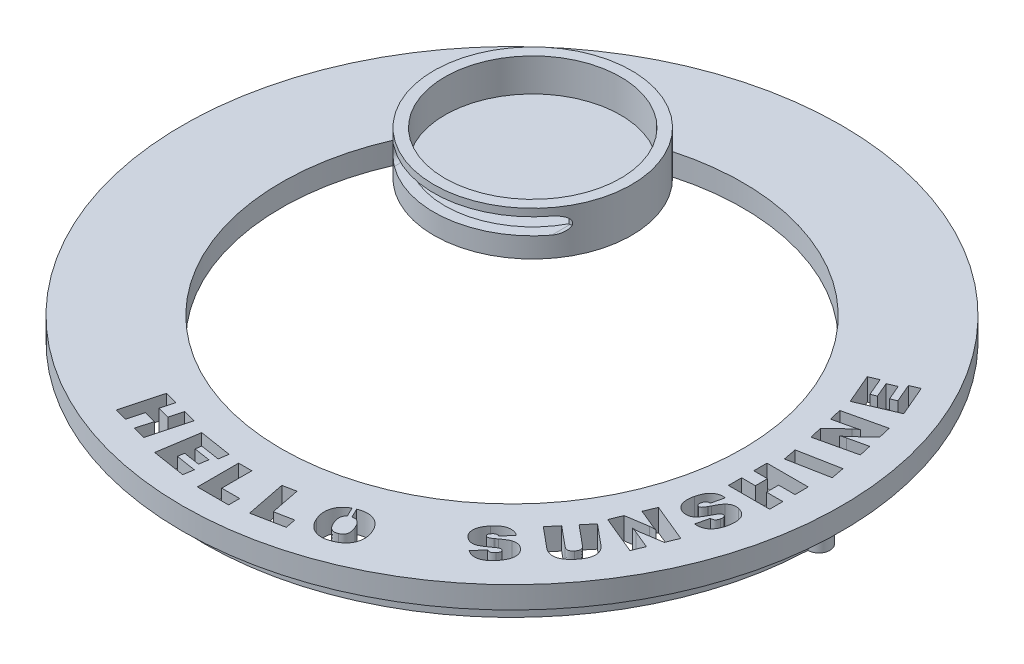
SolidWorks part; units mm, degrees
ref_plane "Front Plane" through (0, 0, 0) normal (0, 0, 1) x (1, 0, 0)
ref_plane "Top Plane" through (0, 0, 0) normal (0, 1, 0) x (1, 0, 0)
ref_plane "Right Plane" through (0, 0, 0) normal (1, 0, 0) x (0, 0, -1)
sketch "Sketch1" plane through (0, 0, 0) normal (0, 1, 0) x (1, 0, 0)
  circle A0 centre (0, 0) radius 30
extrude "Boss-Extrude1" add sketch "Sketch1" along normal blind 2
sketch "Sketch2" plane through (0, 2, 0) normal (0, 1, 0) x (1, 0, 0)
  circle A1 centre (0, 0) radius 21
extrude "Cut-Extrude1" cut sketch "Sketch2" against normal blind 2
sketch "Sketch11" plane through (0, 0, 0) normal (0, 1, 0) x (1, 0, 0)
  circle A0 centre (-11.8757, 13.7636) radius 9
extrude "Boss-Extrude3" add sketch "Sketch11" along normal blind 4
sketch "Sketch13" plane through (0, 4, 0) normal (0, 1, 0) x (1, 0, 0)
  circle A0 centre (-11.8757, 13.7636) radius 8
extrude "Cut-Extrude10" cut sketch "Sketch13" against normal blind 3
sketch "Sketch16" plane through (0, 0, 0) normal (0, 0, 1) x (1, 0, 0)
  line L0 (-17.2913, 2.5788) -> (-4.7087, 2.5788) construction
  line L1 (-17.2913, 3.3288) -> (-4.7087, 3.3288)
  line L2 (-17.2913, 1.8288) -> (-4.7087, 1.8288)
  arc A0 (-17.2913, 3.3288) -> (-17.2913, 1.8288) centre (-17.2913, 2.5788) ccw
  arc A1 (-4.7087, 1.8288) -> (-4.7087, 3.3288) centre (-4.7087, 2.5788) ccw
  point P2 (-11, 2.5788)
extrude "Cut-Extrude13" cut sketch "Sketch16" against normal blind 10
ref_plane "Plane1" through (-19.1926, 2, -8.5231) normal (-0.4059, 0, 0.9139) x (0.9139, 0, 0.4059)
sketch "Sketch18" plane through (0, 2, 0) normal (0, 1, 0) x (1, 0, 0)
  line L0 (1.6808, -27.9014) -> (7.7169, -26.7092) construction
  line L1 (7.7169, -26.7092) -> (13.5209, -24.2959) construction
  line L2 (13.5209, -24.2959) -> (18.5494, -20.5086) construction
  line L3 (18.5494, -20.5086) -> (22.1797, -16.1355) construction
  line L7 (22.1797, -16.1355) -> (24.2924, -12.5872) construction
  line L8 (24.2924, -12.5872) -> (25.8299, -8.8745) construction
  line L9 (25.8299, -8.8745) -> (26.6659, -5.2704) construction
  line L10 (26.6659, -5.2704) -> (27.4225, -2.009) construction
  line L11 (27.4225, -2.009) -> (27.4225, 1.9067) construction
  line L12 (27.4225, 1.9067) -> (26.6659, 5.8673) construction
  line L13 (26.6659, 5.8673) -> (25.8299, 9.4867) construction
  line L14 (25.8299, 9.4867) -> (24.2924, 13.0658) construction
  line L15 (1.6808, -27.9014) -> (-0.6595, -27.9014) construction
  line L16 (-0.6595, -27.9014) -> (-5.0301, -27.2135) construction
  line L17 (-5.0301, -27.2135) -> (-9.5058, -25.995) construction
  line L18 (-9.5058, -25.995) -> (-13.2824, -24.2959) construction
  text T0 "HELLO  SUNSHINE" font "Swis721 Blk BT" height in points 14
extrude "Cut-Extrude16" cut sketch "Sketch18" against normal blind 10
sketch "Sketch19" plane through (0, 2, 0) normal (0, 1, 0) x (1, 0, 0)
  line L0 (8.3141, -23.3105) -> (8.5989, -23.1714)
  line L1 (8.3141, -23.3105) -> (7.8937, -22.4501)
  line L2 (8.5989, -23.1714) -> (8.1785, -22.3109)
  line L3 (7.8937, -22.4501) -> (8.1785, -22.3109)
  spline S0 degree 3 poles (8.5033, -23.2063) (8.4754, -23.2185) (8.4213, -23.2423) (8.3468, -23.2862) (8.2808, -23.3345) (8.2232, -23.3871) (8.1743, -23.4447) (8.1351, -23.5078) (8.1039, -23.5751) (8.0819, -23.6474) (8.0694, -23.725) (8.0651, -23.8082) (8.0693, -23.8972) (8.0814, -23.9922) (8.1029, -24.0929) (8.1327, -24.1994) (8.17, -24.3123) (8.2009, -24.3884) (8.2169, -24.4278) knots 0 0 0 0 0.063426 0.123446 0.179944 0.233994 0.285969 0.337204 0.388463 0.440422 0.494515 0.552142 0.613924 0.680365 0.751975 0.828503 0.911213 1 1 1 1 construction
  spline S1 degree 3 poles (9.5639, -23.8671) (9.5469, -23.8278) (9.5142, -23.7522) (9.4618, -23.6449) (9.4069, -23.5486) (9.3505, -23.4622) (9.292, -23.3865) (9.2327, -23.3201) (9.1708, -23.2649) (9.1071, -23.2198) (9.0409, -23.1847) (8.9722, -23.1592) (8.9008, -23.1419) (8.8263, -23.1365) (8.7492, -23.1396) (8.669, -23.1519) (8.586, -23.1736) (8.5314, -23.1952) (8.5033, -23.2063) knots 0 0 0 0 0.089576 0.172713 0.250093 0.321752 0.388765 0.450476 0.508129 0.562033 0.613713 0.664726 0.715423 0.767057 0.820661 0.876956 0.936694 1 1 1 1 construction
extrude "Boss-Extrude4" add sketch "Sketch19" against normal blind 2
ref_plane "Plane3" through (0, 0, 0) normal (0, -1, 0) x (-1, 0, 0)
sketch "Sketch20" plane through (0, 0, 0) normal (0, 1, 0) x (1, 0, 0)
  circle A0 centre (0, 0) radius 28
extrude "Boss-Extrude8" add sketch "Sketch20" against normal blind 2
sketch "Sketch25" plane through (0, -2, 0) normal (0, -1, 0) x (-1, 0, 0)
  circle A0 centre (0, 0) radius 27
extrude "Cut-Extrude23" cut sketch "Sketch25" against normal blind 2
sketch "Sketch27" plane through (0, -2, 0) normal (0, -1, 0) x (-1, 0, 0)
  line L1 (27.9821, -0.9998) -> (27.9821, 0.9998)
  arc A0 (27.9821, 0.9998) -> (27.9821, -0.9998) centre (28, 0) cw
  circle A1 centre (0, 0) radius 28 construction
extrude "Boss-Extrude10" add sketch "Sketch27" along normal blind 1
sketch "Sketch29" plane through (0, -2, 0) normal (0, -1, 0) x (-1, 0, 0)
  line L0 (-27.9806, -1.041) -> (-27.9836, 0.959)
  arc A0 (-27.9836, 0.959) -> (-27.9806, -1.041) centre (-27.9821, -0.041) ccw
  arc A1 (27.9821, 0.9998) -> (27.9821, -0.9998) centre (0, 0) ccw construction
extrude "Boss-Extrude12" add sketch "Sketch29" against normal blind 1
sketch "Sketch10" plane through (0, 2, 0) normal (0, 1, 0) x (1, 0, 0)
  line L0 (24.3508, 15.4131) -> (22.7341, 17.5903) construction
  line L1 (28.5592, -1.5953) -> (28.5592, 2.5504) construction
  line L2 (28.5592, 2.5504) -> (28.1745, 5.6682) construction
  line L3 (28.1745, 5.6682) -> (27.2714, 9.3985) construction
  line L4 (27.2714, 9.3985) -> (26.1725, 12.2181) construction
  line L5 (26.1725, 12.2181) -> (24.3508, 15.4131) construction
  line L6 (22.7341, 17.5903) -> (20.9299, 20.02) construction
  line L7 (20.9299, 20.02) -> (19.1575, 21.614) construction
  line L8 (19.1575, 21.614) -> (17.029, 23.5282) construction
  line L9 (17.029, 23.5282) -> (14.3036, 25.1267) construction
  text T0 "HELLO  SUNSHINE" font "Century Gothic" height in points 9
